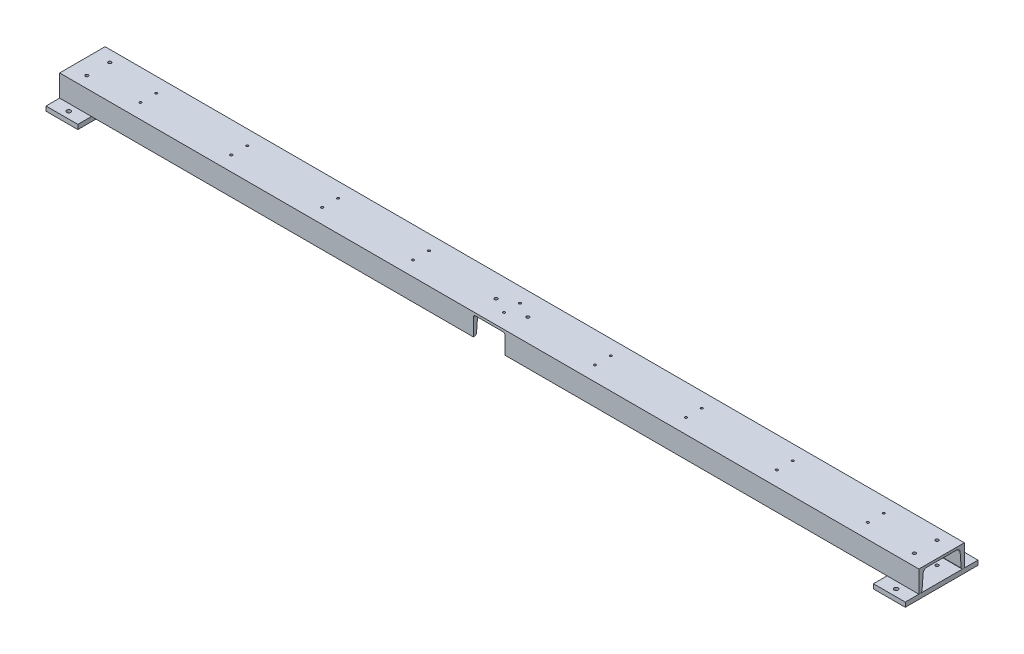
SolidWorks part; units mm, degrees
material "A3钢"
ref_plane "前视基准面" through (0, 0, 0) normal (0, 0, 1) x (1, 0, 0)
ref_plane "上视基准面" through (0, 0, 0) normal (0, 1, 0) x (1, 0, 0)
ref_plane "右视基准面" through (0, 0, 0) normal (1, 0, 0) x (0, 0, -1)
sketch "草图1" plane through (0, 0, 0) normal (0, 0, 1) x (1, 0, 0)
  line L0 (0, 659.1652) -> (0, -626.1553) construction
  line L1 (-1071.9945, 0) -> (1309.6653, 0) construction
  line L2 (-945, 0) -> (945, 0)
  dimension "D1" = 1890
other "槽钢 10(1)"
ref_plane "基准面1" through (-945, 0, 0) normal (1, 0, 0) x (0, 1, 0)
sketch "Sketch1" plane through (-945, 0, 0) normal (1, 0, 0) x (0, 1, 0)
  line L0 (0, 0) -> (0, -100)
  line L1 (0, -100) -> (-48, -100)
  line L2 (0, -50) -> (-5.3, -50) construction
  line L3 (-5.3, -82.1991) -> (-5.3, -17.8009)
  line L4 (-13.1549, -90.6746) -> (-44.0725, -93.0278)
  line L5 (-48, -97.2655) -> (-48, -100)
  line L6 (-5.3, -90.0767) -> (-5.3, -93.3267) construction
  line L7 (-5.3, -93.3267) -> (-48, -93.3267) construction
  line L8 (-24, -100) -> (-24, -91.5) construction
  line L9 (-48, -2.7345) -> (-48, 0)
  line L10 (0, 0) -> (-48, 0)
  line L11 (-13.1549, -9.3254) -> (-44.0725, -6.9722)
  arc A0 (-5.3, -82.1991) -> (-13.1549, -90.6746) centre (-13.8, -82.1991) cw
  arc A1 (-13.1549, -9.3254) -> (-5.3, -17.8009) centre (-13.8, -17.8009) cw
  arc A2 (-44.0725, -93.0278) -> (-48, -97.2655) centre (-43.75, -97.2655) ccw
  arc A3 (-48, -2.7345) -> (-44.0725, -6.9722) centre (-43.75, -2.7345) ccw
  point P2 (-24, 0)
  point P17 (0, 0)
  point P20 (-5.3, -9.9233)
  point P26 (-48, -6.6733)
  dimension "r" = 8.5
  dimension "r1" = 4.25
  dimension "h" = 100
  dimension "b" = 48
  dimension "d" = 5.3
  dimension "t" = 8.5
  dimension "D5" = 42.7
  dimension "D6" = 3.25
sketch "草图2" plane through (0, -48, 0) normal (0, -1, 0) x (1, 0, 0)
  line L0 (-945, -50) -> (-560.3385, -50) construction
  line L1 (-875, -130) -> (-945, -130)
  line L2 (-875, -130) -> (-875, 30)
  line L3 (-875, 30) -> (-945, 30)
  line L4 (-945, -130) -> (-945, 30)
  line L5 (-875, -130) -> (-945, 30) construction
  line L6 (-875, 30) -> (-945, -130) construction
  line L7 (945, 0) -> (-945, 0) construction
  line L8 (945, -100) -> (-945, -100) construction
  point P0 (-910, -50)
  dimension "D1" = 160
  dimension "D2" = 70
extrude "凸台-拉伸1" add sketch "草图2" along normal blind 10 separate body
mirror "镜向3" about plane through (0, 0, 0) normal (1, 0, 0) of bodies 109
sketch "草图3" plane through (0, -48, 0) normal (0, 1, 0) x (1, 0, 0)
  line L0 (-945, 50) -> (945, 50) construction
  line L1 (-945, 100) -> (-945, 0) construction
  line L2 (945, 100) -> (945, 0) construction
  line L3 (0, 100) -> (0, 0) construction
  line L4 (945, 100) -> (-945, 100) construction
  line L5 (945, 0) -> (-945, 0) construction
  line L7 (-910, -15) -> (910, -15)
  line L8 (-910, -15) -> (-910, 115)
  line L9 (-910, 115) -> (910, 115)
  line L10 (910, -15) -> (910, 115)
  line L11 (-910, -15) -> (910, 115) construction
  line L12 (-910, 115) -> (910, -15) construction
  point P12 (0, 50)
  dimension "D1" = 130
  dimension "D2" = 1820
hole_wizard "Ø9.0 (9) 直径孔1" positions "3D草图1" profile "草图4" hole size "Ø9.0" standard "GB" end condition through all
sketch3d "3D草图1"
  point P0 (910, -48, -115)
  point P3 (910, -48, 15)
  point P6 (-910, -48, -115)
  point P9 (-910, -48, 15)
sketch "草图4" plane through (910, -48, -115) normal (1, 0, 0) x (0, 0, 1)
  line L0 (0, 0) -> (0, 10)
  line L1 (0, 10) -> (4.5, 10)
  line L2 (4.5, 10) -> (4.5, 0)
  line L5 (4.5, 0) -> (0, 0)
  line L11 (0, -6.35) -> (0, 107.95) construction
  dimension "通孔孔直径" = 9
  dimension "通孔孔深度" = 10
sketch "草图5" plane through (0, 0, 0) normal (0, 1, 0) x (1, 0, 0)
  line L0 (-945, 50) -> (-441.009, 50) construction
  line L1 (-945, 100) -> (-945, 0) construction
  line L2 (-800, 67.5) -> (-800, 32.5) construction
  dimension "D1" = 145
  dimension "D2" = 35
hole_wizard "M6 螺纹孔1" positions "3D草图2" profile "草图6" tap size "M6" standard "GB" end condition through all
sketch3d "3D草图2"
  point P0 (-800, 0, -32.5)
  point P3 (-800, 0, -67.5)
sketch "草图6" plane through (-800, 0, -32.5) normal (1, 0, 0) x (0, 0, 1)
  line L0 (0, 0) -> (0, 48)
  line L1 (0, 48) -> (2.5, 48)
  line L2 (2.5, 48) -> (2.5, 0)
  line L5 (2.5, 0) -> (0, 0)
  line L11 (0, -6.35) -> (0, 107.95) construction
  dimension "通孔螺纹孔钻头直径" = 5
  dimension "通孔螺纹孔钻头深度" = 48
cosmetic thread "孔螺蚊线1" parameters "D2"=6
cosmetic thread "孔螺蚊线2" parameters "D2"=6
pattern_linear "阵列(线性)1" count 9 spacing 200 along (1, 0, 0) of "M6 螺纹孔1"
sketch "草图7" plane through (0, 0, 0) normal (0, 0, 1) x (1, 0, 0)
  line L1 (945, 0) -> (-945, 0) construction
  line L2 (0, 0) -> (0, -368.4252) construction
  circle A0 centre (0, -24) radius 15
  dimension "D2" = 24
  dimension "D3" = 30
extrude "切除-拉伸1" cut sketch "草图7" against normal up to next
sketch "草图8" plane through (0, 0, 0) normal (0, 0, 1) x (1, 0, 0)
  line L1 (-40, -39) -> (40, -39)
  line L2 (-40, -39) -> (-40, -9)
  line L3 (-40, -9) -> (40, -9)
  line L4 (40, -39) -> (40, -9)
  line L5 (-40, -39) -> (40, -9) construction
  line L6 (-40, -9) -> (40, -39) construction
  point P0 (0, -24)
  dimension "D1" = 80
  dimension "D2" = 30
sketch "草图10" plane through (0, 7.198, -100) normal (0, 0, 1) x (1, 0, 0)
  line L0 (945, -55.198) -> (-945, -55.198) construction
  line L1 (0, -7.198) -> (0, -112.7788) construction
  line L2 (945, -7.198) -> (-945, -7.198) construction
  circle A0 centre (0, -42.198) radius 14
  dimension "D1" = 28
  dimension "D2" = 13
sketch "草图13" plane through (0, 0, 0) normal (0, 0, 1) x (1, 0, 0)
  line L0 (0, 0) -> (0, -193.5705) construction
  line L1 (945, -48) -> (-945, -48) construction
  line L2 (-30, -5.5) -> (30, -5.5)
  line L3 (-35, -10.5) -> (-35, -48)
  line L4 (-35, -48) -> (35, -48)
  line L5 (35, -10.5) -> (35, -48)
  line L6 (-35, -5.5) -> (35, -48) construction
  line L7 (-35, -48) -> (35, -5.5) construction
  arc A0 (30, -5.5) -> (35, -10.5) centre (30, -10.5) cw
  arc A1 (-30, -5.5) -> (-35, -10.5) centre (-30, -10.5) ccw
  point P3 (0, -26.75)
  dimension "D2" = 5
  dimension "D1" = 70
  dimension "D3" = 42.5
extrude "切除-拉伸2" cut sketch "草图13" against normal up to next
extrude "切除-拉伸4" cut sketch "草图10" along normal through all
sketch "草图14" plane through (0, 0, -100) normal (0, 0, -1) x (-1, 0, 0)
  circle A0 centre (0, -35) radius 14 construction
  circle A1 centre (0, -35) radius 14
extrude "凸台-拉伸3" add sketch "草图14" against normal blind 45 separate body
hole_wizard "M22x1.5 螺纹孔1" positions "3D草图4" profile "草图17" tap size "M22x1.5" standard "GB"
sketch3d "3D草图4"
  line L0 (0, -35, -55) -> (0, -35, -100) construction
  point P0 (0, -35, -55)
sketch "草图17" plane through (0, -35, -55) normal (1, 0, 0) x (0, -1, 0)
  line L0 (0, 0) -> (0, 54.6588)
  line L1 (0, 54.6588) -> (10.25, 48.5)
  line L2 (10.25, 48.5) -> (10.25, 0)
  line L5 (10.25, 0) -> (0, 0)
  line L10 (0, 54.6588) -> (-10.25, 48.5) construction
  line L11 (0, -6.35) -> (0, 107.95) construction
  dimension "螺纹孔钻头直径" = 20.5
  dimension "螺纹孔钻头深度" = 48.5
  dimension "导头角度" = 118
cosmetic thread "孔螺蚊线8" parameters "D1"=44, "D2"=22
sketch "草图18" plane through (0, 0, 0) normal (0, 1, 0) x (1, 0, 0)
  line L0 (-945, 50) -> (945, 50) construction
  line L2 (945, 100) -> (945, 0) construction
  line L3 (-945, 100) -> (-945, 0) construction
  line L4 (0, 468.9683) -> (0, -226.5672) construction
  line L6 (-910, 25) -> (910, 25)
  line L7 (-910, 25) -> (-910, 75)
  line L8 (-910, 75) -> (910, 75)
  line L9 (910, 25) -> (910, 75)
  line L10 (-910, 25) -> (910, 75) construction
  line L11 (-910, 75) -> (910, 25) construction
  point P3 (0, 50)
  point P10 (0, 50)
  dimension "D1" = 1820
  dimension "D2" = 50
hole_wizard "M8 螺纹孔1" positions "3D草图5" profile "草图19" tap size "M8" standard "GB" end condition through all
sketch3d "3D草图5"
  point P0 (-910, 0, -75)
  point P3 (-910, 0, -25)
  point P6 (910, 0, -75)
  point P9 (910, 0, -25)
sketch "草图19" plane through (-910, 0, -75) normal (1, 0, 0) x (0, 0, 1)
  line L0 (0, 0) -> (0, 58)
  line L1 (0, 58) -> (3.4, 58)
  line L2 (3.4, 58) -> (3.4, 0)
  line L5 (3.4, 0) -> (0, 0)
  line L11 (0, -6.35) -> (0, 107.95) construction
  dimension "通孔螺纹孔钻头直径" = 6.8
  dimension "通孔螺纹孔钻头深度" = 58
cosmetic thread "孔螺蚊线9" parameters "D2"=8
cosmetic thread "孔螺蚊线10" parameters "D2"=8
cosmetic thread "孔螺蚊线11" parameters "D2"=8
cosmetic thread "孔螺蚊线12" parameters "D2"=8
sketch "草图20" plane through (0, -5.3, 0) normal (0, -1, 0) x (1, 0, 0)
  line L0 (0, 128.8523) -> (0, -128.8523) construction
  line L1 (35, -50) -> (-35, -50) construction
  line L2 (945, -100) -> (-945, -100) construction
  point P4 (0, 0)
  point P7 (19.0182, -51.5321)
  dimension "D1" = 70
  dimension "D2" = 50
hole_wizard "M8 螺纹孔2" positions "3D草图6" profile "草图22" tap size "M8" standard "GB" end condition through all
sketch3d "3D草图6"
  point P0 (35, -5.3, -50)
  point P3 (-35, -5.3, -50)
sketch "草图22" plane through (35, -5.3, -50) normal (1, 0, 0) x (0, 0, -1)
  line L0 (0, 0) -> (0, 5.3)
  line L1 (0, 5.3) -> (3.4, 5.3)
  line L2 (3.4, 5.3) -> (3.4, 0)
  line L5 (3.4, 0) -> (0, 0)
  line L11 (0, -6.35) -> (0, 107.95) construction
  dimension "通孔螺纹孔钻头直径" = 6.8
  dimension "通孔螺纹孔钻头深度" = 5.3
cosmetic thread "孔螺蚊线13" parameters "D2"=8
cosmetic thread "孔螺蚊线14" parameters "D2"=8
